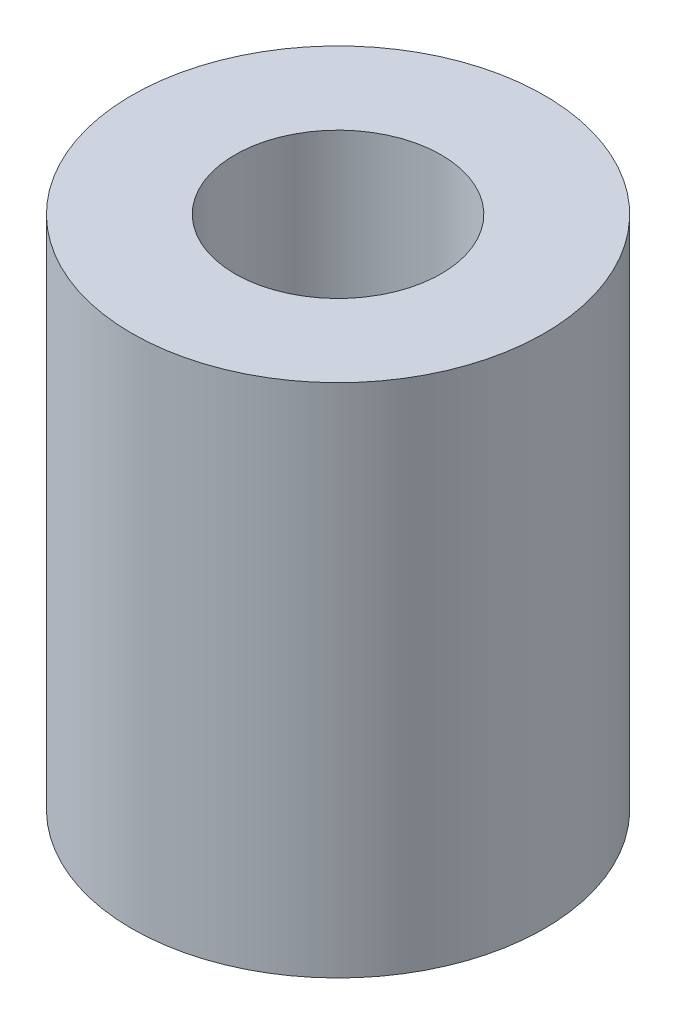
SolidWorks part; units mm, degrees
ref_plane "Front Plane" through (0, 0, 0) normal (0, 0, 1) x (1, 0, 0)
ref_plane "Top Plane" through (0, 0, 0) normal (0, 1, 0) x (1, 0, 0)
ref_plane "Right Plane" through (0, 0, 0) normal (1, 0, 0) x (0, 0, -1)
sketch "Sketch1" plane through (0, 0, 0) normal (0, 1, 0) x (1, 0, 0)
  circle A0 centre (0, 0) radius 2
  circle A1 centre (0, 0) radius 4
  dimension "D1" = 4
  dimension "D2" = 8
extrude "Boss-Extrude1" add sketch "Sketch1" along normal blind 10
